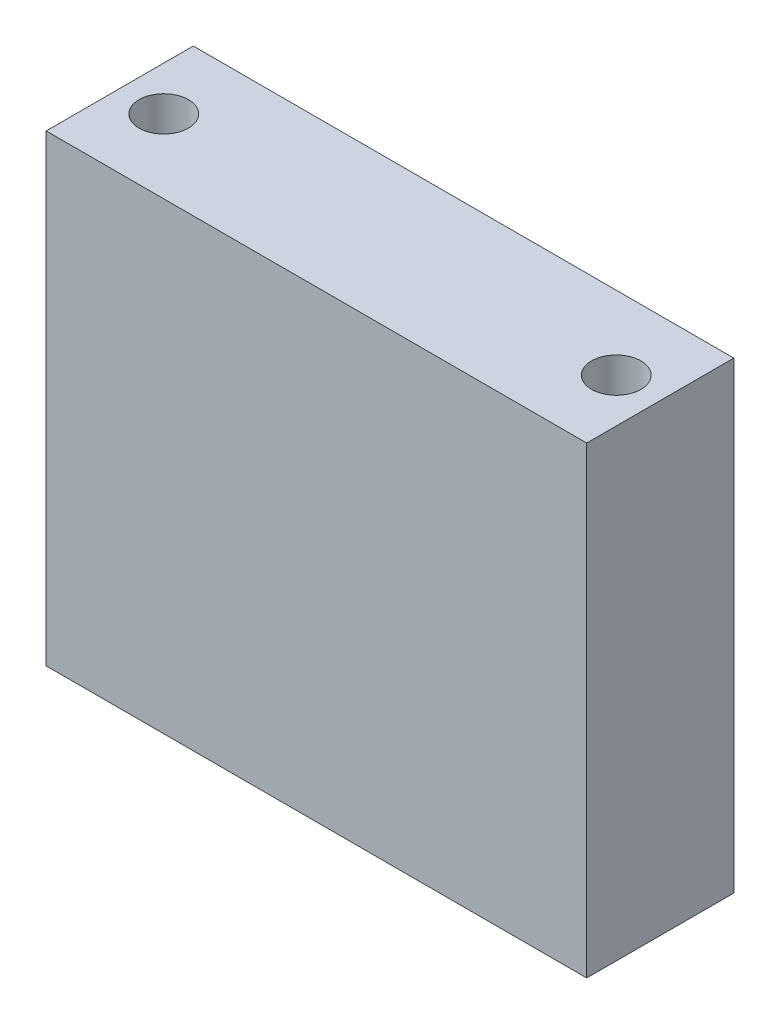
SolidWorks part; units mm, degrees
material "6061-T6 (SS)"
ref_plane "Front" through (0, 0, 0) normal (0, 0, 1) x (1, 0, 0)
ref_plane "Top" through (0, 0, 0) normal (0, 1, 0) x (1, 0, 0)
ref_plane "Right" through (0, 0, 0) normal (1, 0, 0) x (0, 0, -1)
sketch "Sketch1" plane through (0, 0, 0) normal (0, 1, 0) x (1, 0, 0)
  line L0 (-17.5, 4.7625) -> (-17.5, -4.7625)
  line L1 (-17.5, -4.7625) -> (17.5, -4.7625)
  line L2 (17.5, -4.7625) -> (17.5, 4.7625)
  line L3 (17.5, 4.7625) -> (-17.5, 4.7625)
  point P2 (17.5, 0)
  point P5 (0, 4.7625)
extrude "Boss-Extrude1" add sketch "Sketch1" along normal blind 30
hole_wizard "M3 Clearance Hole1" positions "Sketch3" profile "Sketch2" hole size "M3" standard "ANSI Metric" end condition through all
sketch "Sketch3" plane through (0, 30, 0) normal (0, 1, 0) x (1, 0, 0)
  line L3 (-17.5, 4.7625) -> (-17.5, -4.7625) construction
  line L5 (17.5, -4.7625) -> (17.5, 4.7625) construction
  line L6 (17.5, 4.7625) -> (-17.5, 4.7625) construction
  point P0 (14.65, 0)
  point P2 (-14.65, 0)
  point P15 (-17.5, 0)
  dimension "D1" = 2.85
  dimension "D2" = 4.7625
  dimension "D3" = 2.85
sketch "Sketch2" plane through (14.65, 30, 0) normal (1, 0, 0) x (0, 0, 1)
  line L0 (0, 0) -> (0, 30)
  line L1 (0, 30) -> (1.6, 30)
  line L2 (1.6, 30) -> (1.6, 0)
  line L5 (1.6, 0) -> (0, 0)
  line L11 (0, -6.35) -> (0, 107.95) construction
  dimension "Thru Hole Dia." = 3.2
  dimension "Thru Hole Depth" = 30
